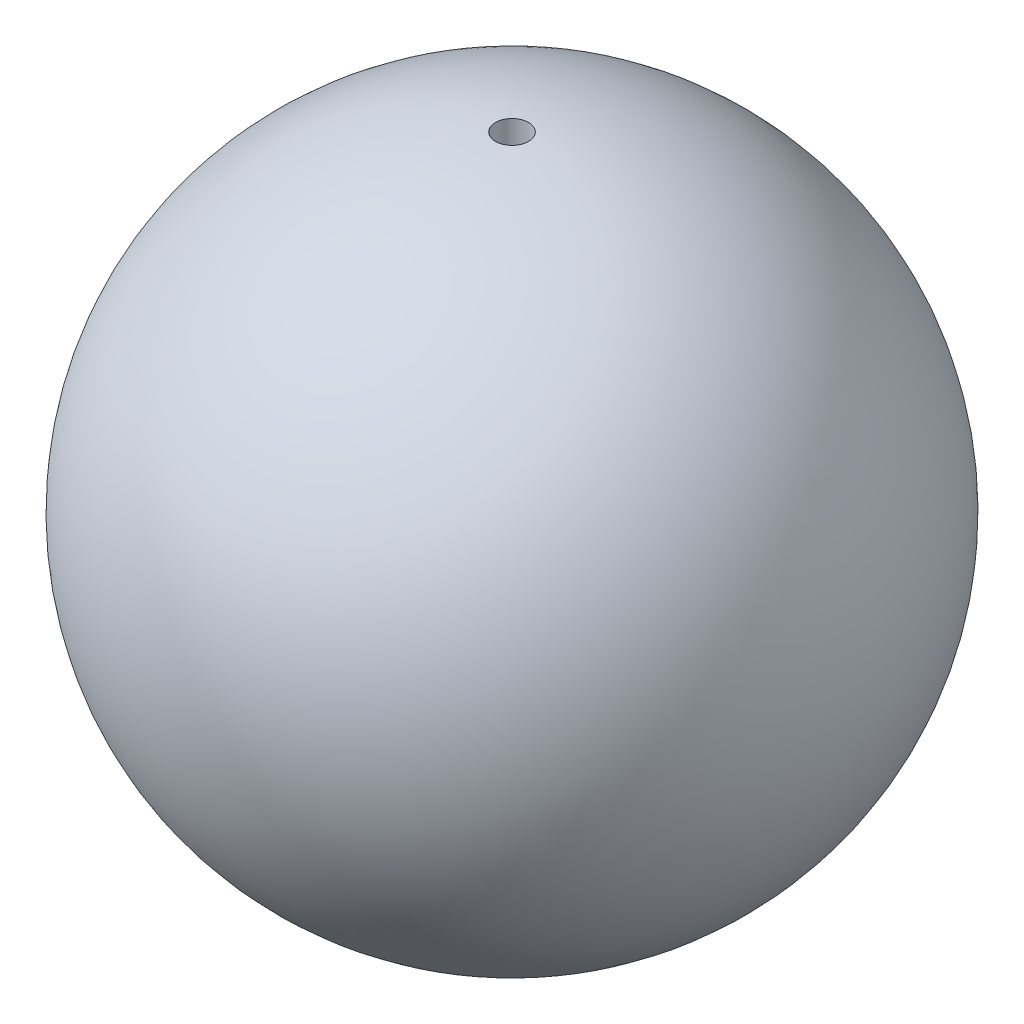
SolidWorks part; units mm, degrees
ref_plane "Front Plane" through (0, 0, 0) normal (0, 0, 1) x (1, 0, 0)
ref_plane "Top Plane" through (0, 0, 0) normal (0, 1, 0) x (1, 0, 0)
ref_plane "Right Plane" through (0, 0, 0) normal (1, 0, 0) x (0, 0, -1)
sketch "Sketch1" plane through (0, 0, 0) normal (0, 1, 0) x (1, 0, 0)
  line L0 (-15.8763, 0) -> (15.1317, 0) construction
  line L1 (-12.5, 0) -> (12.5, 0)
  arc A0 (-12.5, 0) -> (12.5, 0) centre (0, 0) ccw
  dimension "D1" = 12.5
revolve "Revolve5" add sketch "Sketch1" angle 360 about L0
ref_plane "Plane1" through (0, 12.5, 0) normal (0, 1, 0) x (-1, 0, 0)
sketch "Sketch2" plane through (0, 12.5, 0) normal (0, 1, 0) x (-1, 0, 0)
  circle A0 centre (0, 0) radius 0.625
  dimension "D1" = 1.25
extrude "Extrude1" cut sketch "Sketch2" against normal through all
